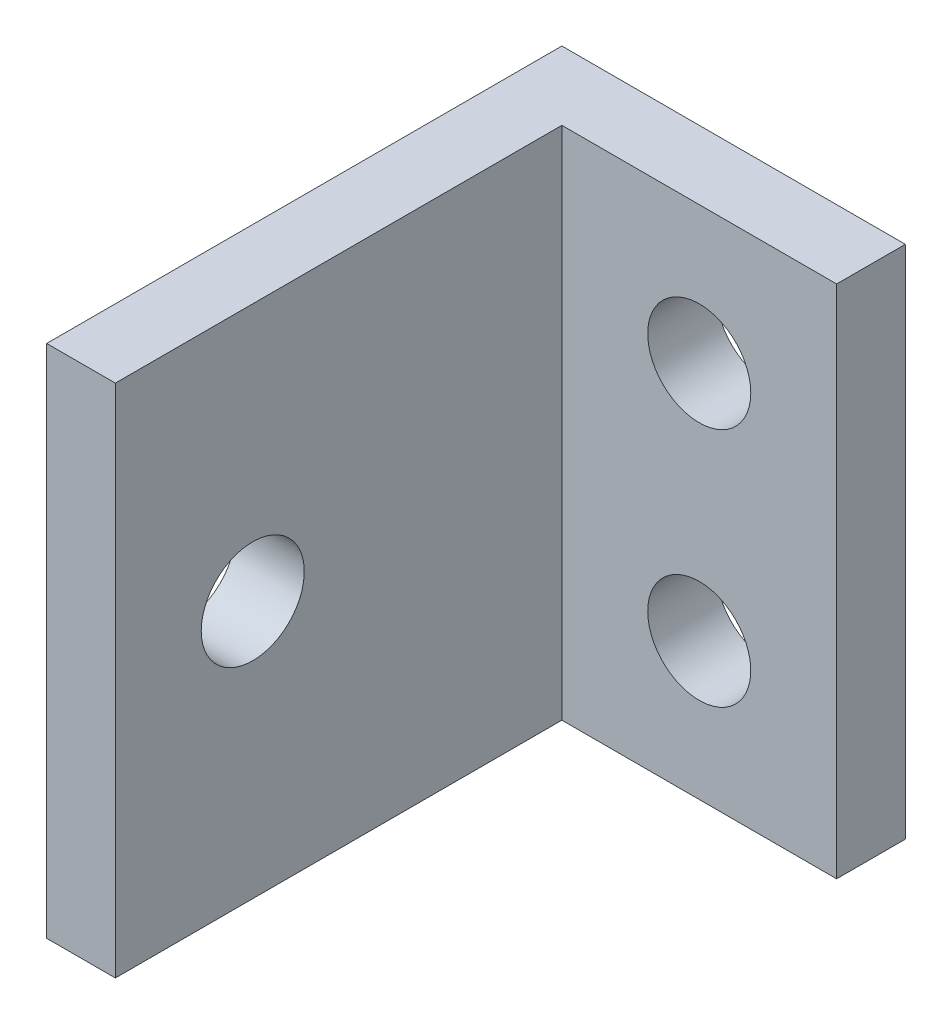
SolidWorks part; units mm, degrees
ref_plane "Front Plane" through (0, 0, 0) normal (0, 0, 1) x (1, 0, 0)
ref_plane "Top Plane" through (0, 0, 0) normal (0, 1, 0) x (1, 0, 0)
ref_plane "Right Plane" through (0, 0, 0) normal (1, 0, 0) x (0, 0, -1)
sketch "Sketch1" plane through (0, 0, 0) normal (0, 1, 0) x (1, 0, 0)
  line L0 (4.4563, 12.5971) -> (-5.5437, 12.5971)
  line L1 (-5.5437, 12.5971) -> (-5.5437, -2.4029)
  line L2 (-5.5437, -2.4029) -> (-3.5437, -2.4029)
  line L3 (-3.5437, -2.4029) -> (-3.5437, 10.5971)
  line L4 (-3.5437, 10.5971) -> (4.4563, 10.5971)
  line L5 (4.4563, 10.5971) -> (4.4563, 12.5971)
  dimension "D1" = 15
  dimension "D2" = 13
  dimension "D3" = 2
  dimension "D4" = 8
extrude "Boss-Extrude1" add sketch "Sketch1" along normal blind 15
sketch "Sketch3" plane through (0, 0, -10.5971) normal (0, 0, 1) x (1, 0, 0)
  line L0 (0.4563, 15) -> (0.4563, 11)
  line L3 (-3.5437, 15) -> (4.4563, 15) construction
  line L4 (4.4563, 7.5) -> (1.0369, 7.5) construction
  line L5 (4.4563, 15) -> (4.4563, 0) construction
  circle A0 centre (0.4563, 11) radius 1.5
  circle A1 centre (0.4563, 4) radius 1.5
  dimension "D1" = 4
  dimension "D2" = 3
extrude "Cut-Extrude1" cut sketch "Sketch3" against normal through all contours A0 | A1
sketch "Sketch4" plane through (-5.5437, 0, 0) normal (-1, 0, 0) x (0, 0, 1)
  line L0 (2.4029, 15) -> (2.4029, 0) construction
  circle A0 centre (-1.5971, 7.5) radius 1.5
  dimension "D1" = 4
extrude "Schnitt-Linear austragen1" cut sketch "Sketch4" against normal blind 10
